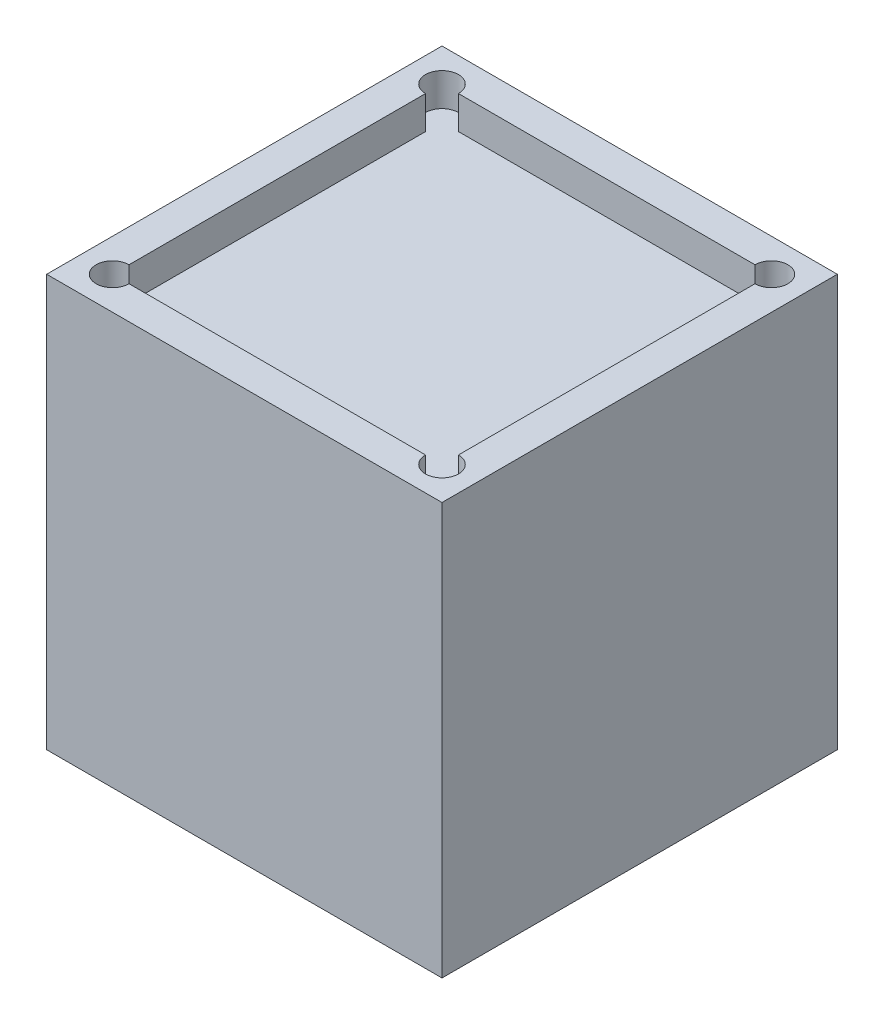
SolidWorks part; units mm, degrees
ref_plane "Front Plane" through (0, 0, 0) normal (0, 0, 1) x (1, 0, 0)
ref_plane "Top Plane" through (0, 0, 0) normal (0, 1, 0) x (1, 0, 0)
ref_plane "Right Plane" through (0, 0, 0) normal (1, 0, 0) x (0, 0, -1)
sketch "Sketch1" plane through (0, 0, 0) normal (0, 1, 0) x (1, 0, 0)
  line L1 (-6, -6) -> (6, -6)
  line L2 (-6, -6) -> (-6, 6)
  line L3 (-6, 6) -> (6, 6)
  line L4 (6, -6) -> (6, 6)
  line L5 (-6, -6) -> (6, 6) construction
  line L6 (-6, 6) -> (6, -6) construction
  point P0 (0, 0)
  dimension "D1" = 12
  dimension "D2" = 12
extrude "Boss-Extrude1" add sketch "Sketch1" along normal blind 11.5
sketch "Sketch2" plane through (0, 11.5, 0) normal (0, 1, 0) x (1, 0, 0)
  line L1 (-5, -5) -> (5, -5)
  line L2 (-5, -5) -> (-5, 5)
  line L3 (-5, 5) -> (5, 5)
  line L4 (5, -5) -> (5, 5)
  line L5 (-5, -5) -> (5, 5) construction
  line L6 (-5, 5) -> (5, -5) construction
  line L7 (6, -6) -> (-6, -6)
  line L8 (6, -6) -> (6, 6)
  line L9 (6, 6) -> (-6, 6)
  line L10 (-6, -6) -> (-6, 6)
  line L11 (6, -6) -> (-6, 6) construction
  line L12 (6, 6) -> (-6, -6) construction
  point P0 (0, 0)
  point P6 (0, 0)
  dimension "D1" = 10
  dimension "D2" = 10
extrude "Boss-Extrude2" add sketch "Sketch2" along normal blind 1
hole_wizard "Ø1.0mm Dowel Hole1" positions "Sketch5" profile "Sketch4" hole size "Ø1.0" standard "ANSI Metric"
sketch "Sketch5" plane through (0, 12.5, 0) normal (0, 1, 0) x (1, 0, 0)
  point P0 (-5, 5)
  point P3 (5, 5)
  point P6 (5, -5)
  point P9 (-5, -5)
sketch "Sketch4" plane through (-5, 12.5, -5) normal (1, 0, 0) x (0, 0, 1)
  line L0 (0, 0) -> (0, 1)
  line L1 (0, 1) -> (0.5, 1)
  line L2 (0.5, 1) -> (0.5, 0)
  line L5 (0.5, 0) -> (0, 0)
  line L10 (0, 1) -> (-0.5, 1) construction
  line L11 (0, -6.35) -> (0, 107.95) construction
  dimension "Hole Dia." = 1
  dimension "Hole Depth" = 1
  dimension "Drill Angle" = 180
sketch "Sketch6" plane through (0, 0, 0) normal (0, -1, 0) x (1, 0, 0)
  line L0 (-6, -6) -> (6, 6) construction
  line L1 (-6, 6) -> (6, 6) construction
  line L2 (3.366, 4.3913) -> (3.9934, 3.764) construction
  line L3 (-3.8851, -3.8723) -> (-3.3193, -4.4381) construction
  line L4 (-6, 6) -> (6, -6) construction
  line L7 (-4.4087, 3.3487) -> (-3.3828, 4.3745) construction
  line L8 (3.1093, -4.6481) -> (4.3745, -3.3828) construction
  dimension "D1" = 3
  dimension "D2" = 3
  dimension "D3" = 3
  dimension "D4" = 3
hole_wizard "1/16 (0.0625) Diameter Hole1" positions "Sketch10" profile "Sketch11" hole size "1/16" standard "ANSI Inch"
sketch "Sketch10" plane through (0, 0, 0) normal (0, -1, 0) x (-1, 0, 0)
  line L0 (6, 6) -> (-6, -6) construction
  line L1 (3.8851, 3.8723) -> (3.3193, 4.4381) construction
  line L2 (-3.366, -4.3913) -> (-3.9934, -3.764) construction
  point P0 (3.8787, 3.8787)
  point P6 (-3.8787, -3.8787)
sketch "Sketch11" plane through (-3.8787, 0, -3.8787) normal (1, 0, 0) x (0, 0, -1)
  line L0 (0, 0) -> (0, 7.5)
  line L1 (0, 7.5) -> (0.7937, 7.5)
  line L2 (0.7937, 7.5) -> (0.7937, 0)
  line L5 (0.7937, 0) -> (0, 0)
  line L10 (0, 7.5) -> (-0.7938, 7.5) construction
  line L11 (0, -6.35) -> (0, 107.95) construction
  dimension "Hole Dia." = 1.5875
  dimension "Hole Depth" = 7.5
  dimension "Drill Angle" = 180
hole_wizard "M2x0.4 Tapped Hole1" positions "Sketch12" profile "Sketch13" tap size "M2x0.4" standard "ANSI Metric"
sketch "Sketch12" plane through (0, 0, 0) normal (0, -1, 0) x (-1, 0, 0)
  line L0 (6, -6) -> (-6, 6) construction
  line L1 (4.4087, -3.3487) -> (3.3828, -4.3745) construction
  line L2 (-3.1093, 4.6481) -> (-4.3745, 3.3828) construction
  point P0 (3.8787, -3.8787)
  point P6 (-3.8787, 3.8787)
sketch "Sketch13" plane through (-3.8787, 0, 3.8787) normal (1, 0, 0) x (0, 0, -1)
  line L0 (0, 0) -> (0, 5.6807)
  line L1 (0, 5.6807) -> (0.8, 5.2)
  line L2 (0.8, 5.2) -> (0.8, 0)
  line L5 (0.8, 0) -> (0, 0)
  line L10 (0, 5.6807) -> (-0.8, 5.2) construction
  line L11 (0, -6.35) -> (0, 107.95) construction
  dimension "Tap Drill Dia." = 1.6
  dimension "Tap Drill Depth" = 5.2
  dimension "Drill Angle" = 118
cosmetic thread "Hole Thread1" parameters "D1"=4, "D2"=2
cosmetic thread "Hole Thread2" parameters "D1"=4, "D2"=2
